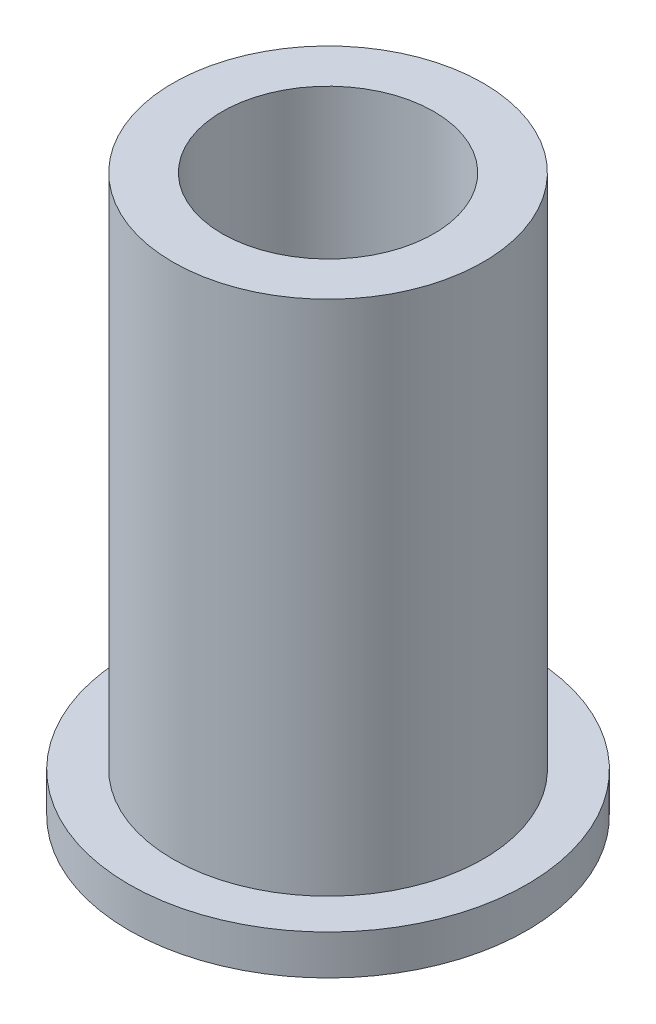
SolidWorks part; units mm, degrees
material "6061-T4 (SS)"
ref_plane "Top" through (0, 0, 0) normal (0, 0, 1) x (1, 0, 0)
ref_plane "Right" through (0, 0, 0) normal (0, 1, 0) x (1, 0, 0)
ref_plane "Front" through (0, 0, 0) normal (1, 0, 0) x (0, 0, -1)
sketch "Sketch1" plane through (0, 0, 0) normal (0, 1, 0) x (1, 0, 0)
  circle A0 centre (0, 0) radius 6.35
  dimension "D1" = 12.7
extrude "Boss-Extrude1" add sketch "Sketch1" along normal blind 1.27
sketch "Sketch2" plane through (0, 1.27, 0) normal (0, 1, 0) x (1, 0, 0)
  circle A0 centre (0, 0) radius 3.3782
  circle A1 centre (0, 0) radius 4.95
  dimension "D1" = 6.7564
  dimension "D2" = 9.9
extrude "Boss-Extrude2" add sketch "Sketch2" along normal blind 16.4996
sketch "Sketch3" plane through (0, 0, 0) normal (0, -1, 0) x (-1, 0, 0)
  circle A0 centre (0, 0) radius 3.3782
  dimension "D1" = 6.7564
extrude "Cut-Extrude1" cut sketch "Sketch3" against normal through all both and the other way through all
